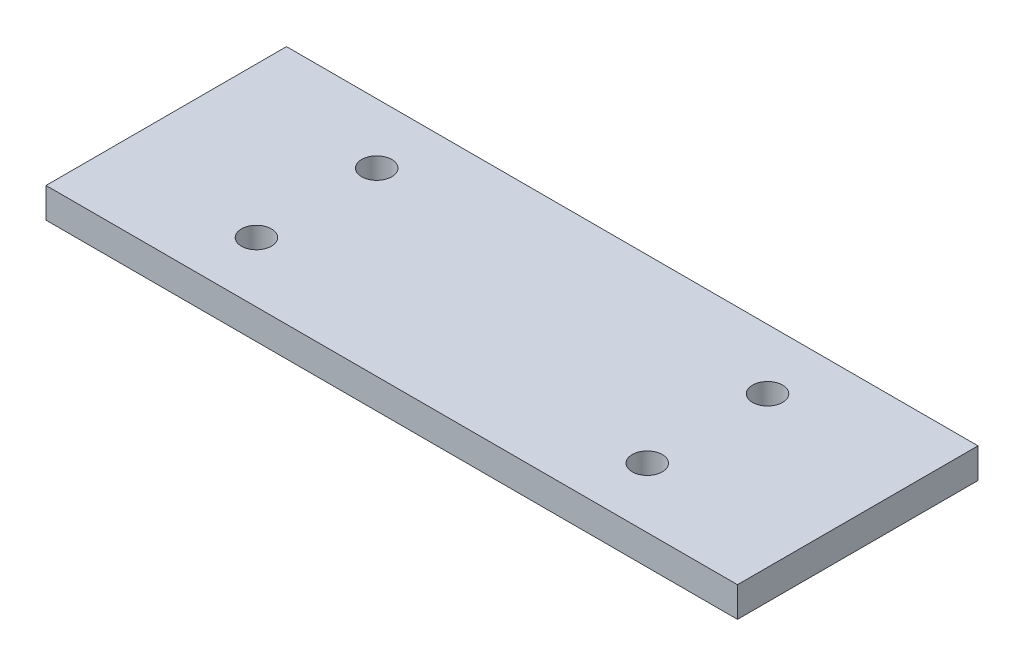
SolidWorks part; units mm, degrees
ref_plane "Front Plane" through (0, 0, 0) normal (0, 0, 1) x (1, 0, 0)
ref_plane "Top Plane" through (0, 0, 0) normal (0, 1, 0) x (1, 0, 0)
ref_plane "Right Plane" through (0, 0, 0) normal (1, 0, 0) x (0, 0, -1)
sketch "Sketch2" plane through (0, 0, 0) normal (0, 1, 0) x (1, 0, 0)
  line L1 (-57.5, -20) -> (57.5, -20)
  line L2 (-57.5, -20) -> (-57.5, 20)
  line L3 (-57.5, 20) -> (57.5, 20)
  line L4 (57.5, -20) -> (57.5, 20)
  line L5 (-57.5, -20) -> (57.5, 20) construction
  line L6 (-57.5, 20) -> (57.5, -20) construction
  circle A0 centre (-32.5, 10) radius 2.5
  circle A1 centre (-32.5, -10) radius 2.5
  circle A2 centre (32.5, 10) radius 2.5
  circle A3 centre (32.5, -10) radius 2.5
  point P0 (0, 0)
  point P14 (0, 0)
  dimension "D3" = 25
  dimension "D1" = 115
  dimension "D2" = 40
  dimension "D4" = 25
  dimension "D5" = 10
  dimension "D6" = 10
  dimension "D7" = 10
  dimension "D8" = 10
  dimension "D9" = 25
  dimension "D10" = 25
extrude "Boss-Extrude2" add sketch "Sketch2" along normal blind 5
